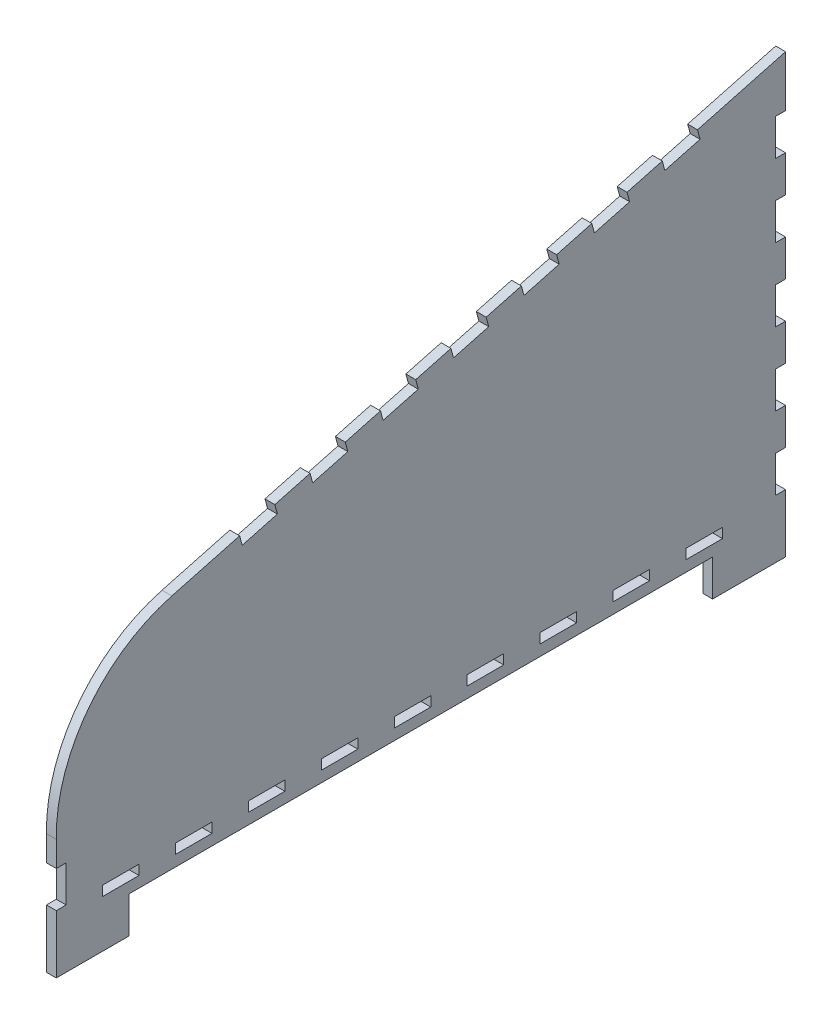
SolidWorks part; units mm, degrees
material "Maple"
ref_plane "Front Plane" through (0, 0, 0) normal (0, 0, 1) x (1, 0, 0)
ref_plane "Top Plane" through (0, 0, 0) normal (0, 1, 0) x (1, 0, 0)
ref_plane "Right Plane" through (0, 0, 0) normal (1, 0, 0) x (0, 0, -1)
sketch "Sketch1" plane through (0, 0, 0) normal (1, 0, 0) x (0, 0, -1)
  line L0 (-100, -60) -> (-80, -60)
  line L1 (-80, -60) -> (-80, -50)
  line L2 (-80, -50) -> (80, -50)
  line L3 (80, -50) -> (80, -60)
  line L4 (80, -60) -> (100, -60)
  line L5 (100, -60) -> (100, 60)
  line L6 (100, 60) -> (-68.3022, 14.9036)
  line L7 (-100, -27.0742) -> (-100, -60)
  line L8 (75.8519, 53.5295) -> (76.5507, 50.9215)
  line L9 (100, -34) -> (97.3, -34)
  line L10 (100, -34) -> (100, -44)
  line L11 (100, -44) -> (97.3, -44)
  line L12 (97.3, -34) -> (97.3, -44)
  line L13 (100, -34) -> (97.3, -44) construction
  line L14 (100, -44) -> (97.3, -34) construction
  line L15 (-100, -44) -> (-97.3, -44)
  line L16 (-100, -44) -> (-100, -34)
  line L17 (-100, -34) -> (-97.3, -34)
  line L18 (-97.3, -44) -> (-97.3, -34)
  line L19 (-100, -44) -> (-97.3, -34) construction
  line L20 (-100, -34) -> (-97.3, -44) construction
  line L21 (76.5507, 50.9215) -> (66.8914, 48.3333)
  line L22 (66.8914, 48.3333) -> (66.1926, 50.9413)
  line L23 (100, -24) -> (97.3, -24)
  line L24 (97.3, -14) -> (97.3, -24)
  line L25 (100, -14) -> (97.3, -14)
  line L26 (100, -4) -> (97.3, -4)
  line L27 (97.3, 6) -> (97.3, -4)
  line L28 (100, 6) -> (97.3, 6)
  line L29 (100, 16) -> (97.3, 16)
  line L30 (97.3, 26) -> (97.3, 16)
  line L31 (100, 26) -> (97.3, 26)
  line L32 (100, 36) -> (97.3, 36)
  line L33 (97.3, 46) -> (97.3, 36)
  line L34 (100, 46) -> (97.3, 46)
  line L35 (100, -44) -> (100, -24) construction
  line L36 (56.5333, 48.3531) -> (57.2321, 45.7451)
  line L37 (57.2321, 45.7451) -> (47.5729, 43.157)
  line L38 (47.5729, 43.157) -> (46.8741, 45.765)
  line L39 (37.2148, 43.1768) -> (37.9136, 40.5688)
  line L40 (37.9136, 40.5688) -> (28.2544, 37.9806)
  line L41 (28.2544, 37.9806) -> (27.5556, 40.5886)
  line L42 (17.8963, 38.0004) -> (18.5951, 35.3924)
  line L43 (18.5951, 35.3924) -> (8.9359, 32.8042)
  line L44 (8.9359, 32.8042) -> (8.237, 35.4122)
  line L45 (-1.4222, 32.824) -> (-0.7234, 30.216)
  line L46 (-0.7234, 30.216) -> (-10.3827, 27.6278)
  line L47 (-10.3827, 27.6278) -> (-11.0815, 30.2358)
  line L48 (-20.7407, 27.6476) -> (-20.0419, 25.0396)
  line L49 (-20.0419, 25.0396) -> (-29.7012, 22.4514)
  line L50 (-29.7012, 22.4514) -> (-30.4, 25.0594)
  line L51 (-40.0592, 22.4712) -> (-39.3604, 19.8632)
  line L52 (-39.3604, 19.8632) -> (-49.0197, 17.275)
  line L53 (-49.0197, 17.275) -> (-49.7185, 19.883)
  line L54 (75.8519, 53.5295) -> (56.5333, 48.3531) construction
  line L55 (-97, -47) -> (80, -47) construction
  line L56 (-80, -47) -> (80, -47) construction
  line L57 (-67.3, -44.3) -> (-67.3, -47)
  line L58 (-87.3, -44.3) -> (-77.3, -44.3)
  line L59 (-87.3, -44.3) -> (-87.3, -47)
  line L60 (-87.3, -47) -> (-77.3, -47)
  line L61 (-77.3, -44.3) -> (-77.3, -47)
  line L62 (-87.3, -44.3) -> (-77.3, -47) construction
  line L63 (-87.3, -47) -> (-77.3, -44.3) construction
  line L64 (-67.3, -44.3) -> (-57.3, -44.3)
  line L65 (-57.3, -44.3) -> (-57.3, -47)
  line L66 (-67.3, -47) -> (-57.3, -47)
  line L67 (-47.3, -44.3) -> (-47.3, -47)
  line L68 (-47.3, -44.3) -> (-37.3, -44.3)
  line L69 (-37.3, -44.3) -> (-37.3, -47)
  line L70 (-47.3, -47) -> (-37.3, -47)
  line L71 (-27.3, -44.3) -> (-27.3, -47)
  line L72 (-27.3, -44.3) -> (-17.3, -44.3)
  line L73 (-17.3, -44.3) -> (-17.3, -47)
  line L74 (-27.3, -47) -> (-17.3, -47)
  line L75 (-7.3, -44.3) -> (-7.3, -47)
  line L76 (-7.3, -44.3) -> (2.7, -44.3)
  line L77 (2.7, -44.3) -> (2.7, -47)
  line L78 (-7.3, -47) -> (2.7, -47)
  line L79 (12.7, -44.3) -> (12.7, -47)
  line L80 (12.7, -44.3) -> (22.7, -44.3)
  line L81 (22.7, -44.3) -> (22.7, -47)
  line L82 (12.7, -47) -> (22.7, -47)
  line L83 (32.7, -44.3) -> (32.7, -47)
  line L84 (32.7, -44.3) -> (42.7, -44.3)
  line L85 (42.7, -44.3) -> (42.7, -47)
  line L86 (32.7, -47) -> (42.7, -47)
  line L87 (52.7, -44.3) -> (52.7, -47)
  line L88 (52.7, -44.3) -> (62.7, -44.3)
  line L89 (62.7, -44.3) -> (62.7, -47)
  line L90 (52.7, -47) -> (62.7, -47)
  line L91 (72.7, -44.3) -> (72.7, -47)
  line L92 (72.7, -44.3) -> (82.7, -44.3)
  line L93 (82.7, -44.3) -> (82.7, -47)
  line L94 (72.7, -47) -> (82.7, -47)
  line L95 (-87.3, -44.3) -> (-67.3, -44.3) construction
  arc A0 (-68.3022, 14.9036) -> (-100, -27.0742) centre (-57.2316, -26.4125) ccw
  point P12 (100, 0)
  point P14 (0, -50)
  point P18 (98.65, -39)
  point P22 (-98.65, -39)
  point P25 (-87.3, -45.65)
  point P83 (-82.3, -45.65)
  dimension "D1" = 75
  dimension "D2" = 200
  dimension "D3" = 20
  dimension "D4" = 20
  dimension "D5" = 120
  dimension "D6" = 42.7735
  dimension "D7" = 10
  dimension "D8" = 2.7
  dimension "D9" = 10
  dimension "D10" = 16
  dimension "D12" = 20
  dimension "D13" = 2.7
  dimension "D14" = 10
  dimension "D15" = 25
  dimension "D17" = 20
  dimension "D18" = 10
  dimension "D19" = 2.7
  dimension "D20" = 16
  dimension "D22" = 10
  dimension "D23" = 2.7
  dimension "D24" = 10
  dimension "D26" = 20
  dimension "D21" = 3
  dimension "D11" = 5
  dimension "D16" = 7
  dimension "D25" = 9
extrude "Boss-Extrude1" add sketch "Sketch1" along normal blind 2.7 contours L6 A0 L7 L17 L18 L15 L0 L1 L2 L3 L4 L5 L11 L12 L9 L23 L24 L25 L26 L27 L28 L29 L30 L31 L32 L33 L34 L8 L21 L22 L36 L37 L38 L39 L40 L41 L42 L43 L44 L45
